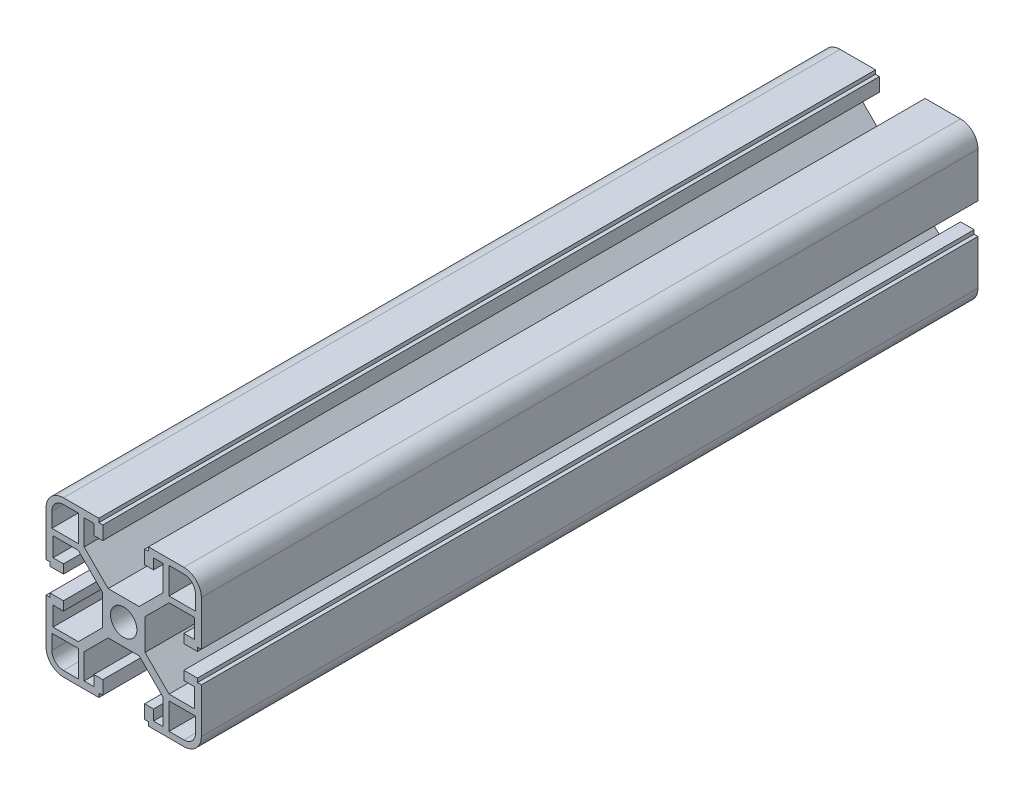
SolidWorks part; units mm, degrees
material "6061-T6 (SS)"
ref_plane "Front Plane" through (0, 0, 0) normal (0, 0, 1) x (1, 0, 0)
ref_plane "Top Plane" through (0, 0, 0) normal (0, 1, 0) x (1, 0, 0)
ref_plane "Right Plane" through (0, 0, 0) normal (1, 0, 0) x (0, 0, -1)
sketch "Sketch1" plane through (0, 0, 0) normal (0, 0, 1) x (1, 0, 0)
  line L0 (3.4, 0) -> (5.5, 0)
  line L1 (10.19, 11.69) -> (4, 5.5)
  line L2 (11.69, 10.19) -> (5.5, 4)
  line L3 (18.2, 10.19) -> (11.69, 10.19)
  line L4 (18.2, 10.19) -> (18.2, 5.2656)
  line L5 (18.2, 5.2656) -> (15.5, 5.2656)
  line L6 (15.5, 5.2656) -> (15.5, 2.9656)
  line L7 (15.5, 2.9656) -> (19, 2.9656)
  line L8 (19, 2.9656) -> (19, 3.9656)
  line L9 (19, 3.9656) -> (20, 3.9656)
  line L10 (20, 3.9656) -> (20, 15.5)
  line L11 (15.5, 20) -> (6.3853, 20)
  line L12 (18.5, 11.69) -> (18.5, 15.5)
  line L13 (15.5, 18.5) -> (11.69, 18.5)
  line L14 (11.69, 11.69) -> (11.69, 18.5)
  line L15 (0, 3.4) -> (0, 5.5)
  line L16 (4, 5.5) -> (0, 5.5)
  line L17 (6.3853, 20) -> (6.3853, 19)
  line L18 (5.5, 0) -> (5.5, 4)
  line L19 (6.3853, 19) -> (5.3853, 19)
  line L20 (5.3853, 19) -> (5.3853, 15.5)
  line L21 (5.3853, 15.5) -> (7.6853, 15.5)
  line L22 (10.19, 11.69) -> (10.19, 18.2)
  line L23 (11.69, 11.69) -> (18.5, 11.69)
  line L24 (7.6853, 18.2) -> (7.6853, 15.5)
  line L25 (10.19, 18.2) -> (7.6853, 18.2)
  arc A0 (20, 15.5) -> (15.5, 20) centre (15.5, 15.5) ccw
  arc A1 (18.5, 15.5) -> (15.5, 18.5) centre (15.5, 15.5) ccw
  arc A2 (3.4, 0) -> (0, 3.4) centre (0, 0) ccw
  dimension "D3" = 4.5
  dimension "D18" = 1.5
  dimension "D9" = 3.4
  dimension "D20" = 1.8
  dimension "D25" = 3
  dimension "D1" = 5.5
  dimension "D2" = 1.5
  dimension "D4" = 14.5
  dimension "D5" = 1.5
  dimension "D6" = 2.1
  dimension "D7" = 2.3
  dimension "D8" = 1.8
  dimension "D10" = 6.81
  dimension "D11" = 2.1
  dimension "D12" = 1
  dimension "D13" = 4.5
  dimension "D14" = 45
  dimension "D15" = 14.5
  dimension "D16" = 1
  dimension "D17" = 1.5
  dimension "D19" = 6.81
  dimension "D21" = 4.5
  dimension "D22" = 2.3
  dimension "D23" = 1
  dimension "D24" = 1
  dimension "D26" = 8.754
  dimension "D27" = 8.754
  dimension "D28" = 4.9244
  dimension "D29" = 2.5047
extrude "Boss-Extrude1" add sketch "Sketch1" along normal blind 200
mirror "Mirror1" about plane through (0, 0, 0) normal (0, 1, 0) of "Boss-Extrude1"
mirror "Mirror2" about plane through (0, 0, 0) normal (1, 0, 0) of "Boss-Extrude1"
mirror "Mirror3" about plane through (0, 0, 0) normal (0, 1, 0) of "Mirror2"
